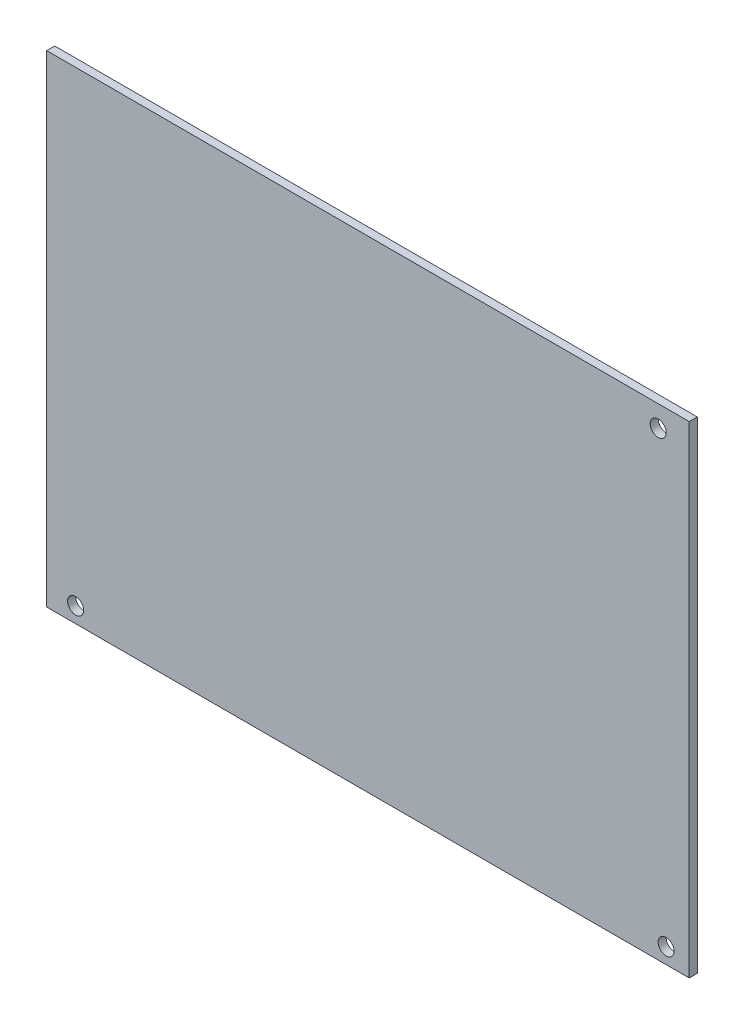
SolidWorks part; units mm, degrees
ref_plane "Front Plane" through (0, 0, 0) normal (0, 0, 1) x (1, 0, 0)
ref_plane "Top Plane" through (0, 0, 0) normal (0, 1, 0) x (1, 0, 0)
ref_plane "Right Plane" through (0, 0, 0) normal (1, 0, 0) x (0, 0, -1)
sketch "Sketch1" plane through (0, 0, 0) normal (0, 0, 1) x (1, 0, 0)
  line L1 (0, 0) -> (160, 0)
  line L2 (0, 0) -> (0, 120)
  line L3 (0, 120) -> (160, 120)
  line L4 (160, 0) -> (160, 120)
  dimension "D1" = 120
  dimension "D2" = 160
extrude "Boss-Extrude1" add sketch "Sketch1" along normal blind 2
sketch "Sketch2" plane through (0, 0, 0) normal (0, 0, -1) x (-1, 0, 0)
  circle A0 centre (-7.1943, 3.8714) radius 2
  circle A1 centre (-154.2403, 3.8714) radius 2
  circle A2 centre (-152.2678, 114.694) radius 2
extrude "Cut-Extrude1" cut sketch "Sketch2" against normal blind 2
